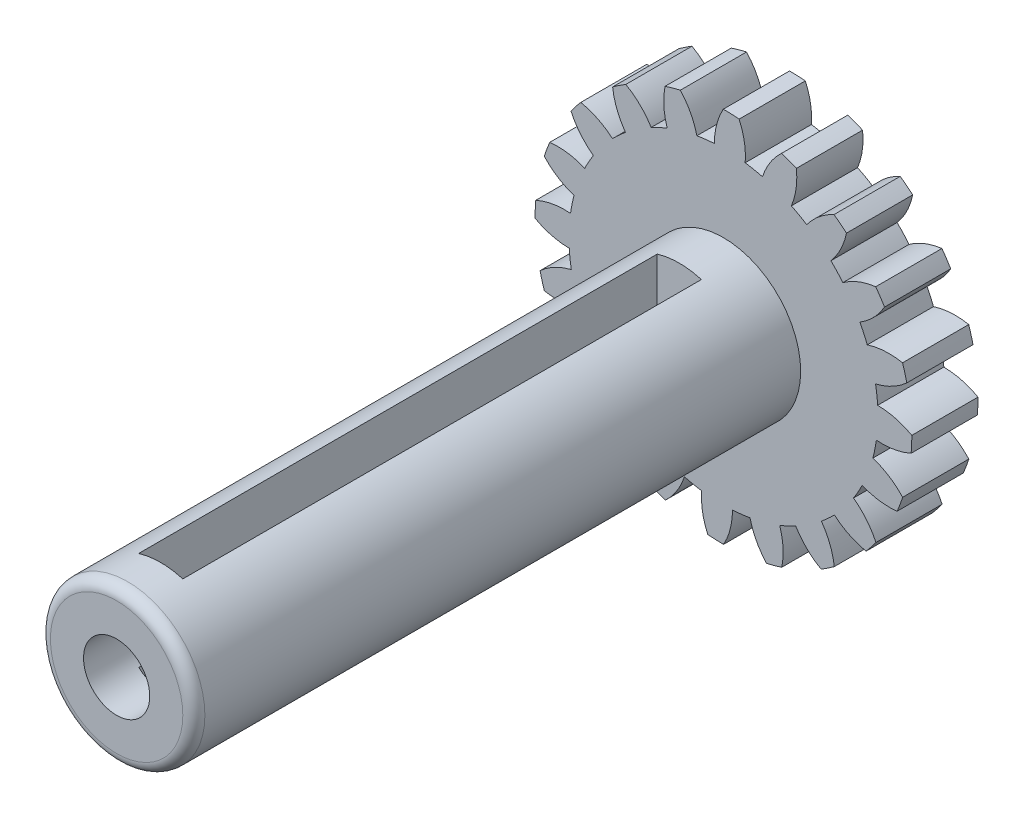
SolidWorks part; units mm, degrees
ref_plane "前视基准面" through (0, 0, 0) normal (0, 0, 1) x (1, 0, 0)
ref_plane "上视基准面" through (0, 0, 0) normal (0, 1, 0) x (1, 0, 0)
ref_plane "右视基准面" through (0, 0, 0) normal (1, 0, 0) x (0, 0, -1)
sketch "草图4" plane through (0, 0, 0) normal (0, 0, 1) x (1, 0, 0)
  arc A0 (6.9869, 0.4108) -> (6.8946, 1.2041) centre (0, 0) ccw
  arc A1 (8.7986, -0.1555) -> (6.9869, 0.4108) centre (6.981, -2.7892) ccw
  arc A2 (8.7815, -0.5703) -> (8.7986, -0.1555) centre (0, 0) ccw
  arc A3 (6.9293, -0.9854) -> (8.7815, -0.5703) centre (7.1871, 2.2042) ccw
  arc A4 (6.7719, -1.7684) -> (6.9293, -0.9854) centre (0, 0) ccw
  arc A5 (8.3199, -2.8668) -> (6.7719, -1.7684) centre (5.7774, -4.8099) ccw
  arc A6 (8.1755, -3.2561) -> (8.3199, -2.8668) centre (0, 0) ccw
  arc A7 (6.2856, -3.0784) -> (8.1755, -3.2561) centre (7.5165, -0.1246) ccw
  arc A8 (5.894, -3.7744) -> (6.2856, -3.0784) centre (0, 0) ccw
  arc A9 (7.0268, -5.2975) -> (5.894, -3.7744) centre (4.0083, -6.3598) ccw
  arc A10 (6.7691, -5.623) -> (7.0268, -5.2975) centre (0, 0) ccw
  arc A11 (5.0267, -4.8701) -> (6.7691, -5.623) centre (7.1101, -2.4413) ccw
  arc A12 (4.4392, -5.4111) -> (5.0267, -4.8701) centre (0, 0) ccw
  arc A13 (5.0459, -7.2096) -> (4.4392, -5.4111) centre (1.8468, -7.2872) ccw
  arc A14 (4.7002, -7.4396) -> (5.0459, -7.2096) centre (0, 0) ccw
  arc A15 (3.2757, -6.1851) -> (4.7002, -7.4396) centre (6.0077, -4.5189) ccw
  arc A16 (2.5498, -6.518) -> (3.2757, -6.1851) centre (0, 0) ccw
  arc A17 (2.571, -8.416) -> (2.5498, -6.518) centre (-0.4954, -7.5012) ccw
  arc A18 (2.1712, -8.5279) -> (2.571, -8.416) centre (0, 0) ccw
  arc A19 (1.2041, -6.8946) -> (2.1712, -8.5279) centre (4.3173, -6.1542) ccw
  arc A20 (0.4108, -6.9869) -> (1.2041, -6.8946) centre (0, 0) ccw
  arc A21 (-0.1555, -8.7986) -> (0.4108, -6.9869) centre (-2.7892, -6.981) ccw
  arc A22 (-0.5703, -8.7815) -> (-0.1555, -8.7986) centre (0, 0) ccw
  arc A23 (-0.9854, -6.9293) -> (-0.5703, -8.7815) centre (2.2042, -7.1871) ccw
  arc A24 (-1.7684, -6.7719) -> (-0.9854, -6.9293) centre (0, 0) ccw
  arc A25 (-2.8668, -8.3199) -> (-1.7684, -6.7719) centre (-4.8099, -5.7774) ccw
  arc A26 (-3.2561, -8.1755) -> (-2.8668, -8.3199) centre (0, 0) ccw
  arc A27 (-3.0784, -6.2856) -> (-3.2561, -8.1755) centre (-0.1246, -7.5165) ccw
  arc A28 (-3.7744, -5.894) -> (-3.0784, -6.2856) centre (0, 0) ccw
  arc A29 (-5.2975, -7.0268) -> (-3.7744, -5.894) centre (-6.3598, -4.0083) ccw
  arc A30 (-5.623, -6.7691) -> (-5.2975, -7.0268) centre (0, 0) ccw
  arc A31 (-4.8701, -5.0267) -> (-5.623, -6.7691) centre (-2.4413, -7.1101) ccw
  arc A32 (-5.4111, -4.4392) -> (-4.8701, -5.0267) centre (0, 0) ccw
  arc A33 (-7.2096, -5.0459) -> (-5.4111, -4.4392) centre (-7.2872, -1.8468) ccw
  arc A34 (-7.4396, -4.7002) -> (-7.2096, -5.0459) centre (0, 0) ccw
  arc A35 (-6.1851, -3.2757) -> (-7.4396, -4.7002) centre (-4.5189, -6.0077) ccw
  arc A36 (-6.518, -2.5498) -> (-6.1851, -3.2757) centre (0, 0) ccw
  arc A37 (-8.416, -2.571) -> (-6.518, -2.5498) centre (-7.5012, 0.4954) ccw
  arc A38 (-8.5279, -2.1712) -> (-8.416, -2.571) centre (0, 0) ccw
  arc A39 (-6.8946, -1.2041) -> (-8.5279, -2.1712) centre (-6.1542, -4.3173) ccw
  arc A40 (-6.9869, -0.4108) -> (-6.8946, -1.2041) centre (0, 0) ccw
  arc A41 (-8.7986, 0.1555) -> (-6.9869, -0.4108) centre (-6.981, 2.7892) ccw
  arc A42 (-8.7815, 0.5703) -> (-8.7986, 0.1555) centre (0, 0) ccw
  arc A43 (-6.9293, 0.9854) -> (-8.7815, 0.5703) centre (-7.1871, -2.2042) ccw
  arc A44 (-6.7719, 1.7684) -> (-6.9293, 0.9854) centre (0, 0) ccw
  arc A45 (-8.3199, 2.8668) -> (-6.7719, 1.7684) centre (-5.7774, 4.8099) ccw
  arc A46 (-8.1755, 3.2561) -> (-8.3199, 2.8668) centre (0, 0) ccw
  arc A47 (-6.2856, 3.0784) -> (-8.1755, 3.2561) centre (-7.5165, 0.1246) ccw
  arc A48 (-5.894, 3.7744) -> (-6.2856, 3.0784) centre (0, 0) ccw
  arc A49 (-7.0268, 5.2975) -> (-5.894, 3.7744) centre (-4.0083, 6.3598) ccw
  arc A50 (-6.7691, 5.623) -> (-7.0268, 5.2975) centre (0, 0) ccw
  arc A51 (-5.0267, 4.8701) -> (-6.7691, 5.623) centre (-7.1101, 2.4413) ccw
  arc A52 (-4.4392, 5.4111) -> (-5.0267, 4.8701) centre (0, 0) ccw
  arc A53 (-5.0459, 7.2096) -> (-4.4392, 5.4111) centre (-1.8468, 7.2872) ccw
  arc A54 (-4.7002, 7.4396) -> (-5.0459, 7.2096) centre (0, 0) ccw
  arc A55 (-3.2757, 6.1851) -> (-4.7002, 7.4396) centre (-6.0077, 4.5189) ccw
  arc A56 (-2.5498, 6.518) -> (-3.2757, 6.1851) centre (0, 0) ccw
  arc A57 (-2.571, 8.416) -> (-2.5498, 6.518) centre (0.4954, 7.5012) ccw
  arc A58 (-2.1712, 8.5279) -> (-2.571, 8.416) centre (0, 0) ccw
  arc A59 (-1.2041, 6.8946) -> (-2.1712, 8.5279) centre (-4.3173, 6.1542) ccw
  arc A60 (-0.4108, 6.9869) -> (-1.2041, 6.8946) centre (0, 0) ccw
  arc A61 (0.1555, 8.7986) -> (-0.4108, 6.9869) centre (2.7892, 6.981) ccw
  arc A62 (0.5703, 8.7815) -> (0.1555, 8.7986) centre (0, 0) ccw
  arc A63 (0.9854, 6.9293) -> (0.5703, 8.7815) centre (-2.2042, 7.1871) ccw
  arc A64 (1.7684, 6.7719) -> (0.9854, 6.9293) centre (0, 0) ccw
  arc A65 (2.8668, 8.3199) -> (1.7684, 6.7719) centre (4.8099, 5.7774) ccw
  arc A66 (3.2561, 8.1755) -> (2.8668, 8.3199) centre (0, 0) ccw
  arc A67 (3.0784, 6.2856) -> (3.2561, 8.1755) centre (0.1246, 7.5165) ccw
  arc A68 (3.7744, 5.894) -> (3.0784, 6.2856) centre (0, 0) ccw
  arc A69 (5.2975, 7.0268) -> (3.7744, 5.894) centre (6.3598, 4.0083) ccw
  arc A70 (5.623, 6.7691) -> (5.2975, 7.0268) centre (0, 0) ccw
  arc A71 (4.8701, 5.0267) -> (5.623, 6.7691) centre (2.4413, 7.1101) ccw
  arc A72 (5.4111, 4.4392) -> (4.8701, 5.0267) centre (0, 0) ccw
  arc A73 (7.2096, 5.0459) -> (5.4111, 4.4392) centre (7.2872, 1.8468) ccw
  arc A74 (7.4396, 4.7002) -> (7.2096, 5.0459) centre (0, 0) ccw
  arc A75 (6.1851, 3.2757) -> (7.4396, 4.7002) centre (4.5189, 6.0077) ccw
  arc A76 (6.518, 2.5498) -> (6.1851, 3.2757) centre (0, 0) ccw
  arc A77 (8.416, 2.571) -> (6.518, 2.5498) centre (7.5012, -0.4954) ccw
  arc A78 (8.5279, 2.1712) -> (8.416, 2.571) centre (0, 0) ccw
  arc A79 (6.8946, 1.2041) -> (8.5279, 2.1712) centre (6.1542, 4.3173) ccw
  circle A81 centre (0, 0) radius 8.5361
extrude "凸台-拉伸4" add sketch "草图4" along normal blind 3 contours A79 A81 A77 A76 A75 A73 A72 A71 A69 A68 A67 A65 A64 A63 A61 A60 A59 A57 A56 A55 A53 A52 A51 A49 A48 A47 A45 A44 A43 A41 A40 A39 A37 A36 A35 A33 A32 A31 A29
sketch "草图5" plane through (0, 0, 3) normal (0, 0, 1) x (1, 0, 0)
  circle A0 centre (0, 0) radius 3.5
extrude "凸台-拉伸6" add sketch "草图5" along normal blind 27.5
sketch "草图8" plane through (0, 0, 30.5) normal (0, 0, 1) x (1, 0, 0)
  circle A0 centre (0, 0) radius 1.5
extrude "切除-拉伸1" cut sketch "草图8" against normal blind 10
sketch "草图10" plane through (0, 0, 0) normal (0, 1, 0) x (1, 0, 0)
  line L0 (3.5, -30.5) -> (3.5, -3) construction
  line L1 (-1, -5) -> (1, -5)
  line L2 (-1, -5) -> (-1, -28.5)
  line L3 (-1, -28.5) -> (1, -28.5)
  line L4 (1, -5) -> (1, -28.5)
  dimension "D1" = 2
  dimension "D2" = 2
  dimension "D3" = 2
  dimension "D4" = 2.5
extrude "切除-拉伸2" cut sketch "草图10" against normal mid plane 10
fillet "圆角1" radius 0.5 1 edges at (3.5, 0, 30.5)
